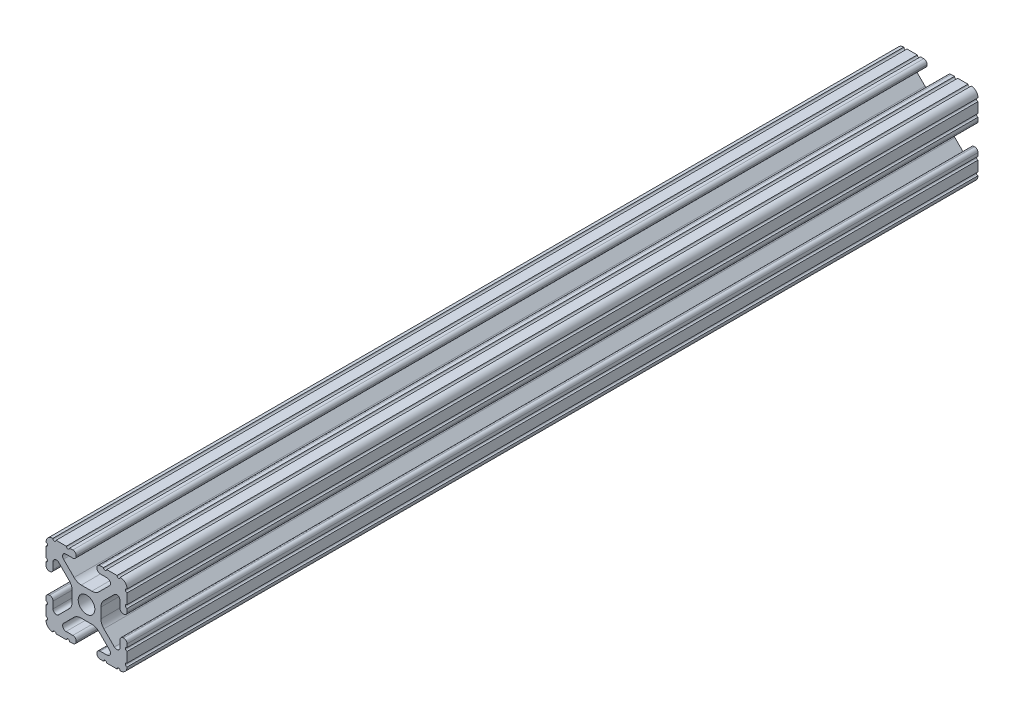
SolidWorks part; units mm, degrees
ref_plane "Front Plane" through (0, 0, 0) normal (0, 0, 1) x (1, 0, 0)
ref_plane "Top Plane" through (0, 0, 0) normal (0, 1, 0) x (1, 0, 0)
ref_plane "Right Plane" through (0, 0, 0) normal (1, 0, 0) x (0, 0, -1)
sketch "Sketch1" plane through (0, 0, 0) normal (0, 0, 1) x (1, 0, 0)
  line L0 (-7.207, 8.7244) -> (-3.8983, 5.4232)
  line L1 (-4.2875, 10.4902) -> (-6.4768, 10.4902)
  line L2 (-3.2385, 11.651) -> (-3.2385, 11.5392)
  line L3 (-5.3171, 12.7) -> (-4.2875, 12.7)
  line L4 (0, 13.4005) -> (0, -14.8534) construction
  line L5 (12.7, 0) -> (-13.9989, 0) construction
  line L6 (-9.5504, 12.7) -> (-6.3331, 12.7)
  line L7 (-12.7, 6.3331) -> (-12.7, 9.5504)
  line L8 (-12.7, 4.2875) -> (-12.7, 5.3171)
  line L9 (-11.5392, 3.2385) -> (-11.651, 3.2385)
  line L10 (-10.4902, 6.4021) -> (-10.4902, 4.2875)
  line L11 (-5.441, 3.8408) -> (-8.7371, 7.1294)
  line L12 (-4.5085, -1.5932) -> (-4.5085, 1.5932)
  line L13 (-1.7093, -4.4958) -> (1.7093, -4.4958)
  line L14 (3.9523, -5.4237) -> (7.1797, -8.6452)
  line L15 (6.4164, -10.4902) -> (4.2875, -10.4902)
  line L16 (3.2385, -11.5392) -> (3.2385, -11.651)
  line L17 (4.2875, -12.7) -> (5.3171, -12.7)
  line L18 (6.3331, -12.7) -> (9.5504, -12.7)
  line L19 (12.7, -9.5504) -> (12.7, -6.3331)
  line L20 (12.7, -5.3171) -> (12.7, -4.2875)
  line L21 (11.651, -3.2385) -> (11.5392, -3.2385)
  line L22 (10.4902, -4.2875) -> (10.4902, -6.4021)
  line L23 (8.7371, -7.1294) -> (5.441, -3.8408)
  line L24 (4.5085, -1.5932) -> (4.5085, 1.5932)
  line L25 (5.441, 3.8408) -> (8.7371, 7.1294)
  line L26 (10.4902, 6.4021) -> (10.4902, 4.2875)
  line L27 (11.5392, 3.2385) -> (11.651, 3.2385)
  line L28 (12.7, 4.2875) -> (12.7, 5.3171)
  line L29 (12.7, 6.3331) -> (12.7, 9.5504)
  line L30 (9.5504, 12.7) -> (6.3331, 12.7)
  line L31 (5.3171, 12.7) -> (4.2875, 12.7)
  line L32 (3.2385, 11.651) -> (3.2385, 11.5392)
  line L33 (4.2875, 10.4902) -> (6.4768, 10.4902)
  line L34 (7.207, 8.7244) -> (3.8983, 5.4232)
  line L35 (1.6558, 4.4958) -> (-1.6558, 4.4958)
  line L36 (-8.7371, -7.1294) -> (-5.441, -3.8408)
  line L37 (-10.4902, -4.2875) -> (-10.4902, -6.4021)
  line L38 (-11.651, -3.2385) -> (-11.5392, -3.2385)
  line L39 (-12.7, -5.3171) -> (-12.7, -4.2875)
  line L40 (-12.7, -9.5504) -> (-12.7, -6.3331)
  line L41 (-6.3331, -12.7) -> (-9.5504, -12.7)
  line L42 (-4.2875, -12.7) -> (-5.3171, -12.7)
  line L43 (-3.2385, -11.5392) -> (-3.2385, -11.651)
  line L44 (-6.4164, -10.4902) -> (-4.2875, -10.4902)
  line L45 (-3.9523, -5.4237) -> (-7.1797, -8.6452)
  arc A0 (-7.207, 8.7244) -> (-6.4768, 10.4902) centre (-6.4768, 9.4563) cw
  arc A1 (-3.2385, 11.5392) -> (-4.2875, 10.4902) centre (-4.2875, 11.5392) cw
  arc A2 (-4.2875, 12.7) -> (-3.2385, 11.651) centre (-4.2875, 11.651) cw
  arc A3 (-5.3171, 12.7) -> (-6.3331, 12.7) centre (-5.8251, 12.7) cw
  arc A4 (-9.5504, 12.7) -> (-10.5664, 12.6998) centre (-10.0584, 12.7) cw
  arc A5 (-12.6998, 10.5664) -> (-10.5664, 12.6998) centre (-10.5918, 10.5918) cw
  arc A6 (-12.6998, 10.5664) -> (-12.7, 9.5504) centre (-12.7, 10.0584) cw
  arc A7 (-12.7, 6.3331) -> (-12.7, 5.3171) centre (-12.7, 5.8251) cw
  arc A8 (-11.651, 3.2385) -> (-12.7, 4.2875) centre (-11.651, 4.2875) cw
  arc A9 (-10.4902, 4.2875) -> (-11.5392, 3.2385) centre (-11.5392, 4.2875) cw
  circle A10 centre (0, 0) radius 2.6035
  arc A11 (-10.4902, 6.4021) -> (-8.7371, 7.1294) centre (-9.4628, 6.4021) cw
  arc A12 (-5.441, 3.8408) -> (-4.5085, 1.5932) centre (-7.6835, 1.5932) cw
  arc A13 (-4.5085, -1.5932) -> (-5.441, -3.8408) centre (-7.6835, -1.5932) cw
  arc A14 (-8.7371, -7.1294) -> (-10.4902, -6.4021) centre (-9.4628, -6.4021) cw
  arc A15 (-1.7093, -4.4958) -> (-3.9523, -5.4237) centre (-1.7093, -7.6708) ccw
  arc A16 (3.9523, -5.4237) -> (1.7093, -4.4958) centre (1.7093, -7.6708) ccw
  arc A17 (6.4164, -10.4902) -> (7.1797, -8.6452) centre (6.4164, -9.4098) ccw
  arc A18 (4.2875, -10.4902) -> (3.2385, -11.5392) centre (4.2875, -11.5392) ccw
  arc A19 (3.2385, -11.651) -> (4.2875, -12.7) centre (4.2875, -11.651) ccw
  arc A20 (6.3331, -12.7) -> (5.3171, -12.7) centre (5.8251, -12.7) ccw
  arc A21 (10.5664, -12.6998) -> (9.5504, -12.7) centre (10.0584, -12.7) ccw
  arc A22 (10.5664, -12.6998) -> (12.6998, -10.5664) centre (10.5918, -10.5918) ccw
  arc A23 (12.7, -9.5504) -> (12.6998, -10.5664) centre (12.7, -10.0584) ccw
  arc A24 (12.7, -5.3171) -> (12.7, -6.3331) centre (12.7, -5.8251) ccw
  arc A25 (12.7, -4.2875) -> (11.651, -3.2385) centre (11.651, -4.2875) ccw
  arc A26 (11.5392, -3.2385) -> (10.4902, -4.2875) centre (11.5392, -4.2875) ccw
  arc A27 (8.7371, -7.1294) -> (10.4902, -6.4021) centre (9.4628, -6.4021) ccw
  arc A28 (4.5085, -1.5932) -> (5.441, -3.8408) centre (7.6835, -1.5932) ccw
  arc A29 (5.441, 3.8408) -> (4.5085, 1.5932) centre (7.6835, 1.5932) ccw
  arc A30 (10.4902, 6.4021) -> (8.7371, 7.1294) centre (9.4628, 6.4021) ccw
  arc A31 (10.4902, 4.2875) -> (11.5392, 3.2385) centre (11.5392, 4.2875) ccw
  arc A32 (11.651, 3.2385) -> (12.7, 4.2875) centre (11.651, 4.2875) ccw
  arc A33 (12.7, 6.3331) -> (12.7, 5.3171) centre (12.7, 5.8251) ccw
  arc A34 (12.6998, 10.5664) -> (12.7, 9.5504) centre (12.7, 10.0584) ccw
  arc A35 (12.6998, 10.5664) -> (10.5664, 12.6998) centre (10.5918, 10.5918) ccw
  arc A36 (9.5504, 12.7) -> (10.5664, 12.6998) centre (10.0584, 12.7) ccw
  arc A37 (5.3171, 12.7) -> (6.3331, 12.7) centre (5.8251, 12.7) ccw
  arc A38 (4.2875, 12.7) -> (3.2385, 11.651) centre (4.2875, 11.651) ccw
  arc A39 (3.2385, 11.5392) -> (4.2875, 10.4902) centre (4.2875, 11.5392) ccw
  arc A40 (7.207, 8.7244) -> (6.4768, 10.4902) centre (6.4768, 9.4563) ccw
  arc A41 (1.6558, 4.4958) -> (3.8983, 5.4232) centre (1.6558, 7.6708) ccw
  arc A42 (-1.6558, 4.4958) -> (-3.8983, 5.4232) centre (-1.6558, 7.6708) cw
  arc A43 (-11.5392, -3.2385) -> (-10.4902, -4.2875) centre (-11.5392, -4.2875) cw
  arc A44 (-12.7, -4.2875) -> (-11.651, -3.2385) centre (-11.651, -4.2875) cw
  arc A45 (-12.7, -5.3171) -> (-12.7, -6.3331) centre (-12.7, -5.8251) cw
  arc A46 (-12.7, -9.5504) -> (-12.6998, -10.5664) centre (-12.7, -10.0584) cw
  arc A47 (-10.5664, -12.6998) -> (-12.6998, -10.5664) centre (-10.5918, -10.5918) cw
  arc A48 (-10.5664, -12.6998) -> (-9.5504, -12.7) centre (-10.0584, -12.7) cw
  arc A49 (-6.3331, -12.7) -> (-5.3171, -12.7) centre (-5.8251, -12.7) cw
  arc A50 (-3.2385, -11.651) -> (-4.2875, -12.7) centre (-4.2875, -11.651) cw
  arc A51 (-4.2875, -10.4902) -> (-3.2385, -11.5392) centre (-4.2875, -11.5392) cw
  arc A52 (-6.4164, -10.4902) -> (-7.1797, -8.6452) centre (-6.4164, -9.4098) cw
  dimension "D1" = 5.207
  dimension "D9" = 14.859
  dimension "D2" = 25.4
  dimension "D3" = 12.7
  dimension "D4" = 6.477
  dimension "D5" = 8.2042
  dimension "D6" = 9.017
  dimension "D8" = 2.2098
  dimension "D10" = 2.2098
extrude "Extrude1" add sketch "Sketch1" against normal blind 266.7
